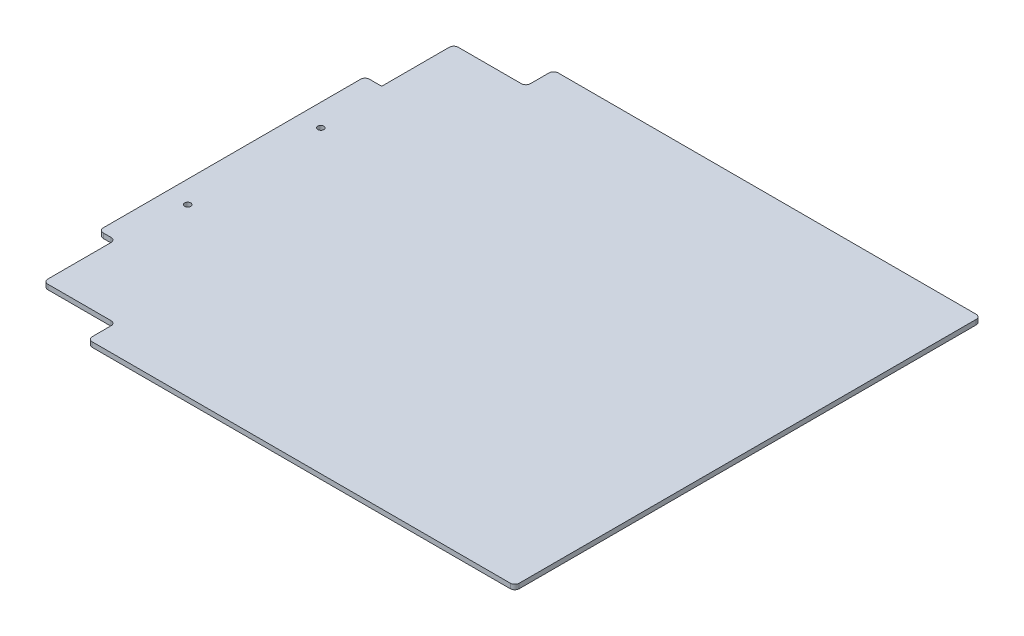
SolidWorks part; units mm, degrees
ref_plane "Front Plane" through (0, 0, 0) normal (0, 0, 1) x (1, 0, 0)
ref_plane "Top Plane" through (0, 0, 0) normal (0, 1, 0) x (1, 0, 0)
ref_plane "Right Plane" through (0, 0, 0) normal (1, 0, 0) x (0, 0, -1)
sketch "Sketch1" plane through (0, 0, 0) normal (0, 1, 0) x (1, 0, 0)
  line L1 (0, 0) -> (304.8, 0)
  line L2 (0, 0) -> (0, 304.8)
  line L3 (0, 304.8) -> (304.8, 304.8)
  line L4 (304.8, 0) -> (304.8, 304.8)
  dimension "D1" = 304.8
  dimension "D2" = 304.8
extrude "Boss-Extrude1" add sketch "Sketch1" along normal blind 2.7781
sketch "Sketch2" plane through (0, 2.7781, 0) normal (0, 1, 0) x (1, 0, 0)
  line L0 (304.8, 0) -> (304.8, 304.8) construction
  line L1 (0, 0) -> (304.8, 0)
  line L2 (0, 0) -> (0, 19.05)
  line L3 (0, 19.05) -> (304.8, 19.05)
  line L4 (304.8, 0) -> (304.8, 19.05)
  line L6 (0, 304.8) -> (304.8, 304.8)
  line L7 (0, 304.8) -> (0, 285.75)
  line L8 (0, 285.75) -> (304.8, 285.75)
  line L9 (304.8, 304.8) -> (304.8, 285.75)
  dimension "D1" = 19.05
  dimension "D2" = 19.05
extrude "Cut-Extrude1" cut sketch "Sketch2" against normal through all
sketch "Sketch3" plane through (0, 2.7781, 0) normal (0, 1, 0) x (1, 0, 0)
  line L0 (0, 285.75) -> (304.8, 285.75) construction
  line L1 (50.8, 285.75) -> (0, 285.75)
  line L2 (50.8, 285.75) -> (50.8, 269.875)
  line L3 (50.8, 269.875) -> (9.525, 269.875)
  line L5 (0, 285.75) -> (0, 19.05) construction
  line L6 (0, 19.05) -> (0, 76.2)
  line L9 (0, 228.6) -> (9.525, 228.6)
  line L10 (9.525, 269.875) -> (9.525, 228.6)
  line L11 (0, 76.2) -> (9.525, 76.2)
  line L12 (9.525, 76.2) -> (9.525, 34.925)
  line L13 (9.525, 34.925) -> (50.8, 34.925)
  line L14 (50.8, 34.925) -> (50.8, 19.05)
  line L15 (304.8, 19.05) -> (0, 19.05) construction
  line L16 (50.8, 19.05) -> (0, 19.05)
  line L18 (0, 285.75) -> (0, 228.6)
  dimension "D1" = 50.8
  dimension "D2" = 57.15
  dimension "D3" = 9.525
  dimension "D4" = 15.875
  dimension "D5" = 50.8
  dimension "D6" = 57.15
  dimension "D7" = 15.875
  dimension "D8" = 9.525
extrude "Cut-Extrude2" cut sketch "Sketch3" against normal through all
sketch "Sketch4" plane through (0, 2.7781, 0) normal (0, 1, 0) x (1, 0, 0)
  line L0 (304.8, 19.05) -> (50.8, 19.05) construction
  line L1 (0, 228.6) -> (0, 76.2) construction
  circle A0 centre (12.7, 190.5762) radius 1.7526
  circle A1 centre (12.7, 114.3762) radius 1.7526
  dimension "D1" = 3.5052
  dimension "D4" = 12.7
  dimension "D2" = 76.2
  dimension "D3" = 95.3262
extrude "Cut-Extrude3" cut sketch "Sketch4" against normal through all
sketch "Sketch5" plane through (0, 2.7781, 0) normal (0, 1, 0) x (1, 0, 0)
  line L0 (304.8, 19.05) -> (50.8, 19.05) construction
  line L1 (304.8, 285.75) -> (295.275, 285.75)
  line L2 (304.8, 285.75) -> (304.8, 19.05)
  line L3 (304.8, 19.05) -> (295.275, 19.05)
  line L4 (295.275, 285.75) -> (295.275, 19.05)
  dimension "D1" = 9.525
extrude "Cut-Extrude4" cut sketch "Sketch5" against normal through all
fillet "Fillet1" radius 2.54 11 edges at (295.275, 1.3891, -285.75) (295.275, 1.3891, -19.05) (50.8, 1.3891, -19.05) (50.8, 1.3891, -34.925) (9.525, 1.3891, -76.2) (9.525, 1.3891, -34.925) (0, 1.3891, -76.2) (0, 1.3891, -228.6) (50.8, 1.3891, -285.75) (50.8, 1.3891, -269.875) (9.525, 1.3891, -269.875)
